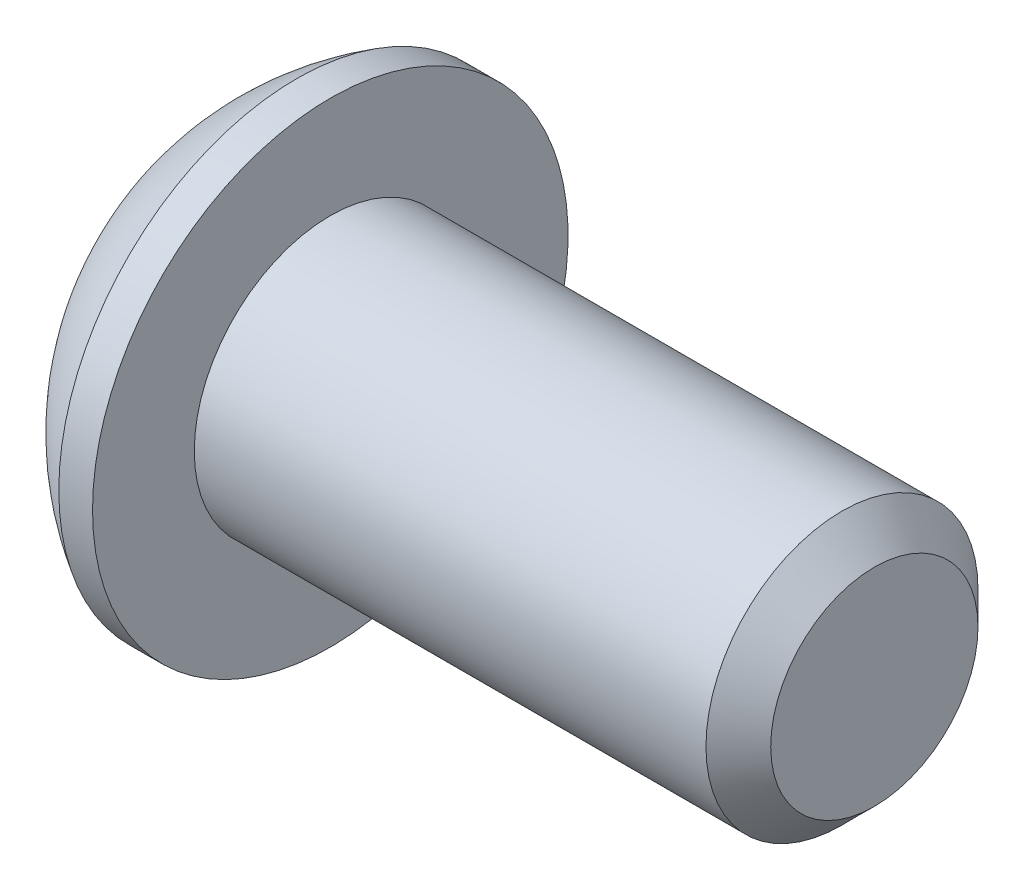
SolidWorks part; units mm, degrees
ref_plane "Plane1"
ref_plane "Plane2" through (0, 0, 0) normal (0, 1, 0) x (1, 0, 0)
ref_plane "Plane3" through (0, 0, 0) normal (1, 0, 0) x (0, 0, -1)
sketch "BodySke" plane through (0, 0, 0) normal (0, 0, 1) x (1, 0, 0)
  line L0 (16.0528, 0) -> (16.0528, 2.4193)
  line L1 (15.2971, 3.175) -> (3.3528, 3.175)
  line L2 (3.3528, 3.175) -> (3.3528, 5.5499)
  line L3 (3.3528, 5.5499) -> (2.5654, 5.5499)
  line L4 (0, 0) -> (101.6, 0) construction
  line L5 (3.3528, -5.5499) -> (2.5654, -5.5499) construction
  line L6 (55.6768, -3.175) -> (3.3528, -3.175) construction
  line L7 (16.0528, 0) -> (0, 0)
  line L8 (0, 2.775) -> (0, -2.775) construction
  line L9 (0, 0) -> (0, 2.775)
  line L10 (16.0528, 2.4193) -> (15.2971, 3.175)
  line L11 (16.0528, -2.4193) -> (15.2971, -3.175) construction
  line L12 (4.6228, 9.525) -> (4.6228, -3.175) construction
  line L13 (3.3528, 9.525) -> (3.3528, -3.175) construction
  arc A1 (0, 2.775) -> (2.5654, 5.5499) centre (5.7851, 0) cw
  dimension "D1" = 5.5499
  dimension "Diameter" = 6.35
  dimension "Length" = 12.7
  dimension "Head_dia" = 11.0998
  dimension "Head_ht" = 3.3528
  dimension "Head_side_ht" = 0.7874
  dimension "Minor_dia" = 4.8387
  dimension "Body_ch_ang" = 45
  dimension "Advance" = 1.27
  dimension "Thread_nom" = 12.7
revolve "BaseBody" add sketch "BodySke" angle 360 about L4
cosmetic thread "ThreadCosmetic" parameters "Thread_length"=11.43, "Thread_minor"=4.8387
sketch "Sketch2" plane through (0, 0, 0) normal (0, 0, 1) x (1, 0, 0)
  line L0 (0, 1.9812) -> (2.2098, 1.9812)
  line L1 (2.2098, 1.9812) -> (3.3536, 0)
  line L3 (3.3536, 0) -> (0, 0)
  line L4 (0, 0) -> (0, 1.9812)
  line L5 (0, -1.9812) -> (2.2098, -1.9812) construction
  line L6 (0, 0) -> (47.625, 0) construction
  dimension "D2" = 60
  dimension "PreBroach_depth" = 2.2098
  dimension "PreBroach_dia" = 3.9624
revolve "PreBroach" cut sketch "Sketch2" angle 360 about L6
sketch "Sketch3" plane through (0, 0, 0) normal (1, 0, 0) x (0, 0, -1)
  line L0 (-1.9812, -1.1438) -> (-1.9812, 1.1438)
  line L1 (-1.9812, 1.1438) -> (0, 2.2877)
  line L2 (0, 2.2877) -> (1.9812, 1.1438)
  line L3 (1.9812, 1.1438) -> (1.9812, -1.1438)
  line L4 (1.9812, -1.1438) -> (0, -2.2877)
  line L5 (0, -2.2877) -> (-1.9812, -1.1438)
  dimension "D1" = 1.9812
  dimension "D2" = 1.9812
  dimension "D3" = 3.9624
  dimension "Hex_size" = 3.9624
extrude "Hex" cut sketch "Sketch3" along normal blind 2.2098
sketch "Sketch4" plane through (0, 9.525, 0) normal (1, 0, 0) x (0, 0, -1)
  line L0 (0, -9.525) -> (2.3876, -9.525)
  line L1 (0, -9.525) -> (6.1484, -5.9752) construction
  line L2 (0, -9.525) -> (1.1938, -7.4573)
  line L3 (1.9883, -8.949) -> (2.2704, -8.7861)
  line L4 (1.493, -8.0911) -> (1.7751, -7.9282)
  arc A0 (1.9883, -8.949) -> (1.493, -8.0911) centre (0, -9.525) ccw
  arc A1 (2.3876, -9.525) -> (2.2704, -8.7861) centre (0, -9.525) ccw
  arc A2 (1.1938, -7.4573) -> (1.7751, -7.9282) centre (0, -9.525) cw
  dimension "D1" = 30
  dimension "Spline_n_dim" = 4.1402
  dimension "Spline_m_dim" = 4.7752
  dimension "D2" = 60
  dimension "D3" = 0.4953
  dimension "Spline_p_dim" = 0.9906
extrude "Spline" [suppressed] cut sketch "Sketch4" along normal blind 2.2098
pattern_circular "CirPattern1" [suppressed] count 6 every 60 about axis through (0, 0, 0) along (1, 0, 0)
sketch "ThdSchSke" plane through (0, 0, 0) normal (0, 0, 1) x (1, 0, 0)
  line L0 (4.6228, -2.4193) -> (4.0937, -3.175)
  line L1 (4.6228, -2.4193) -> (5.1519, -3.175)
  line L2 (5.1519, -3.175) -> (5.1519, -3.9688)
  line L3 (-3.175, 0) -> (5.1513, 0) construction
  line L4 (0, 1.1438) -> (0, 2.2877) construction
  line L5 (5.1519, -3.9688) -> (4.0937, -3.9688)
  line L6 (4.0937, -3.9688) -> (4.0937, -3.175)
  dimension "Thread_minor" = 4.8387
  dimension "Diameter" = 6.35
  dimension "Start" = 4.6228
  dimension "SideAngle" = 55
  dimension "VeeAngle" = 70
  dimension "Overcut" = 7.9375
revolve "ThreadSchematic" [suppressed] cut sketch "ThdSchSke" angle 360 about L3
pattern_linear "ThdSchPat" [suppressed]
equation "\"D1@BodySke\" = \"Head_dia@BodySke\" * .5"
equation "\"Thread_minor@ThreadCosmetic\" = \"Minor_dia@BodySke\""
equation "\"D1@Sketch3\" = \"Hex_size@Sketch3\" / 2"
equation "\"D2@Sketch3\" = \"D1@Sketch3\""
equation "\"D3@Sketch3\" = \"Hex_size@Sketch3\""
equation "\"D3@Sketch4\" = \"Spline_p_dim@Sketch4\" / 2"
equation "\"D1@Sketch4\" = \"D2@Sketch4\" / 2"
equation "\"Thread_length@ThreadCosmetic\" = ((sgn( (\"Length@BodySke\" - \"Advance@BodySke\" ) - \"Thread_nom@BodySke\" )-1)*( (\"Length@BodySke\" - \"Advance@BodySke\" ) - \"Thread_nom@BodySke\" ))/-2+ \"Thread_nom@BodySke\""
equation "\"Thread_minor@ThdSchSke\" = \"Minor_dia@BodySke\""
equation "\"Diameter@ThdSchSke\" = \"Diameter@BodySke\""
equation "\"Overcut@ThdSchSke\" = \"Diameter@BodySke\" * 1.25"
equation "\"Start@ThdSchSke\" = \"Head_ht@BodySke\" + \"Length@BodySke\" - \"Thread_length@ThreadCosmetic\"  '---Non-countersunk---"
equation "\"Num_threads@ThdSchPat\" = int( \"Thread_length@ThreadCosmetic\" / \"Advance@BodySke\" + 0.999 )  + 1"
equation "\"Advance@ThdSchPat\" = \"Thread_length@ThreadCosmetic\" /  (\"Num_threads@ThdSchPat\" - 1) 'relax it"
equation "\"Num_threads@ThdSchPat\" = \"Num_threads@ThdSchPat\" - sgn( \"Num_threads@ThdSchPat\" - 1) '---chamfered tips only---"
